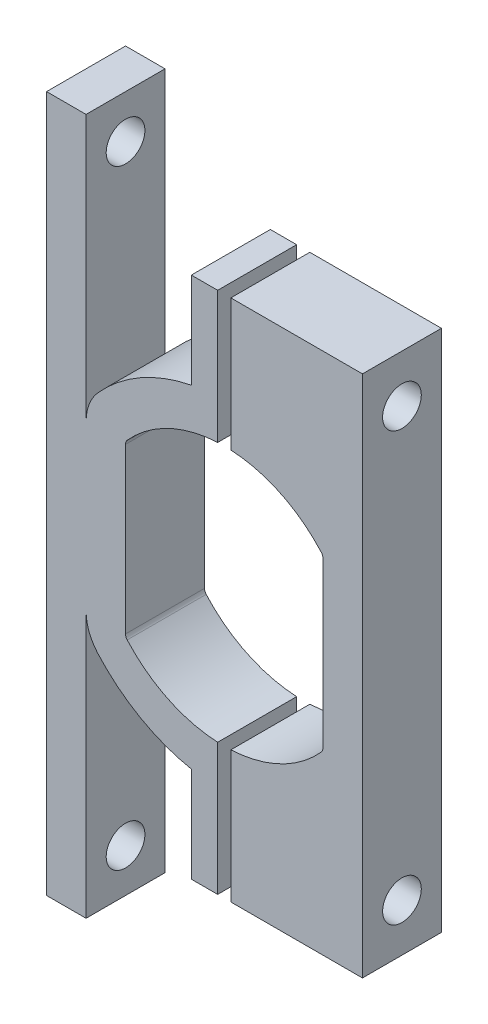
SolidWorks part; units mm, degrees
ref_plane "Front Plane" through (0, 0, 0) normal (0, 0, 1) x (1, 0, 0)
ref_plane "Top Plane" through (0, 0, 0) normal (0, 1, 0) x (1, 0, 0)
ref_plane "Right Plane" through (0, 0, 0) normal (1, 0, 0) x (0, 0, -1)
sketch "Sketch1" plane through (0, 0, 0) normal (0, 0, 1) x (1, 0, 0)
  line L1 (-32.5, -32.5) -> (32.5, -32.5)
  line L2 (-32.5, -32.5) -> (-32.5, 32.5)
  line L3 (-32.5, 32.5) -> (32.5, 32.5)
  line L4 (32.5, -32.5) -> (32.5, 32.5)
  line L5 (-32.5, -32.5) -> (32.5, 32.5) construction
  line L6 (-32.5, 32.5) -> (32.5, -32.5) construction
  point P0 (0, 0)
  dimension "D1" = 65
extrude "Boss-Extrude1" add sketch "Sketch1" along normal blind 6
sketch "Sketch3" plane through (0, 0, 6) normal (0, 0, 1) x (1, 0, 0)
  line L0 (28.5, 4.5979) -> (28.5, 6.2362) construction
  line L1 (28.5, -4.5979) -> (28.5, 4.5979) construction
  line L2 (28.5, -6.2362) -> (28.5, -4.5979) construction
  line L3 (13.5, -4.5979) -> (13.5, -6.2362) construction
  line L4 (13.5, 4.5979) -> (13.5, -4.5979) construction
  line L5 (13.5, 6.2362) -> (13.5, 4.5979) construction
  line L6 (28.5, 4.5979) -> (28.5, 6.2362)
  line L7 (28.5, -4.5979) -> (28.5, 4.5979)
  line L8 (28.5, -6.2362) -> (28.5, -4.5979)
  line L9 (13.5, -4.5979) -> (13.5, -6.2362)
  line L10 (13.5, 4.5979) -> (13.5, -4.5979)
  line L11 (13.5, 6.2362) -> (13.5, 4.5979)
  line L18 (10.5, 6.2362) -> (10.5, 4.5979)
  line L19 (10.5, 4.5979) -> (10.5, -4.5979)
  line L21 (10.5, -4.5979) -> (10.5, -6.2362)
  line L22 (31.5, -6.2362) -> (31.5, -4.5979)
  line L27 (31.5, 4.5979) -> (31.5, 6.2362)
  line L41 (31.5, -4.5979) -> (31.5, 4.5979) construction
  arc A0 (28.5, 6.2362) -> (28.3733, 6.5688) centre (28, 6.2362) ccw construction
  arc A1 (28.3733, -6.5688) -> (28.5, -6.2362) centre (28, -6.2362) ccw construction
  arc A2 (13.6267, -6.5688) -> (28.3733, -6.5688) centre (21, 0) ccw construction
  arc A3 (13.5, -6.2362) -> (13.6267, -6.5688) centre (14, -6.2362) ccw construction
  arc A4 (13.6267, 6.5688) -> (13.5, 6.2362) centre (14, 6.2362) ccw construction
  arc A5 (28.3733, 6.5688) -> (13.6267, 6.5688) centre (21, 0) ccw construction
  arc A6 (28.5, 6.2362) -> (28.3733, 6.5688) centre (28, 6.2362) ccw
  arc A7 (28.3733, -6.5688) -> (28.5, -6.2362) centre (28, -6.2362) ccw
  arc A8 (13.6267, -6.5688) -> (28.3733, -6.5688) centre (21, 0) ccw
  arc A9 (13.5, -6.2362) -> (13.6267, -6.5688) centre (14, -6.2362) ccw
  arc A10 (13.6267, 6.5688) -> (13.5, 6.2362) centre (14, 6.2362) ccw
  arc A11 (28.3733, 6.5688) -> (13.6267, 6.5688) centre (21, 0) ccw
  arc A18 (31.5, 6.2362) -> (30.6133, 8.5644) centre (28, 6.2362) ccw
  arc A19 (30.6133, 8.5644) -> (11.3867, 8.5644) centre (21, 0) ccw
  arc A20 (11.3867, 8.5644) -> (10.5, 6.2362) centre (14, 6.2362) ccw
  arc A21 (10.5, -6.2362) -> (11.3867, -8.5644) centre (14, -6.2362) ccw
  arc A22 (11.3867, -8.5644) -> (30.6133, -8.5644) centre (21, 0) ccw
  arc A23 (30.6133, -8.5644) -> (31.5, -6.2362) centre (28, -6.2362) ccw
  dimension "D1" = 3
extrude "Cut-Extrude2" cut sketch "Sketch3" against normal blind 10
sketch "Sketch4" plane through (0, 0, 0) normal (0, 0, -1) x (-1, 0, 0)
  line L0 (-21, 12.875) -> (-21, 19.875)
  line L1 (-21, 19.875) -> (-18.5, 19.875)
  line L2 (-18.5, 19.875) -> (-18.5, 12.6299)
  line L3 (-31.5, 6.2362) -> (-31.5, 19.875)
  line L4 (-31.5, 19.875) -> (-21, 19.875)
  line L5 (3.3, 0) -> (-3.3, 0) construction
  line L6 (-31.5, -19.875) -> (-21, -19.875)
  line L7 (-31.5, -6.2362) -> (-31.5, -19.875)
  line L8 (-18.5, -19.875) -> (-18.5, -12.6299)
  line L9 (-21, -19.875) -> (-18.5, -19.875)
  line L10 (-21, -12.875) -> (-21, -19.875)
  arc A0 (-11.3867, 8.5644) -> (-30.6133, 8.5644) centre (-21, 0) ccw construction
  arc A1 (-30.6133, 8.5644) -> (-31.5, 6.2362) centre (-28, 6.2362) ccw construction
  arc A2 (-30.6133, 8.5644) -> (-31.5, 6.2362) centre (-28, 6.2362) ccw
  arc A3 (-18.5, 12.6299) -> (-30.6133, 8.5644) centre (-21, 0) ccw
  arc A4 (-30.6133, -8.5644) -> (-31.5, -6.2362) centre (-28, -6.2362) cw
  arc A5 (-18.5, -12.6299) -> (-30.6133, -8.5644) centre (-21, 0) cw
  arc M16 (-30.6133, 8.5644) -> (-31.5, 6.2362) centre (-28, 6.2362) ccw
  arc M23 (-11.3867, 8.5644) -> (-30.6133, 8.5644) centre (-21, 0) ccw
  dimension "D1" = 7
  dimension "D2" = 2.5
extrude "Boss-Extrude2" add sketch "Sketch4" against normal up to surface (6 mm away) contours L4 L3 L0 M16 M23 | L2 L1 L0 M23 | L9 L8 A5 A4 L7 L6 up to face at (21, 0, 6)
sketch "Sketch6" plane through (0, 0, 6) normal (0, 0, 1) x (1, 0, 0)
  line L0 (21, 9.875) -> (21, 19.875)
  line L1 (18.5, 19.875) -> (31.5, 19.875) construction
  line L2 (21.5, 19.875) -> (20.5, 19.875)
  line L3 (21.5, 19.875) -> (21.5, 9.8623)
  line L4 (20.5, 19.875) -> (20.5, 9.8623)
  line L5 (3.3, 0) -> (-3.3, 0) construction
  line L6 (20.5, -19.875) -> (20.5, -9.8623)
  line L7 (21.5, -19.875) -> (21.5, -9.8623)
  line L8 (21.5, -19.875) -> (20.5, -19.875)
  line L9 (21, -9.875) -> (21, -19.875)
  arc A0 (28.3733, 6.5688) -> (13.6267, 6.5688) centre (21, 0) ccw construction
  arc A1 (21.5, 9.8623) -> (20.5, 9.8623) centre (21, 0) ccw
  arc A2 (21.5, -9.8623) -> (20.5, -9.8623) centre (21, 0) cw
  point P11 (21, 19.875)
  dimension "D1" = 1
extrude "Cut-Extrude3" cut sketch "Sketch6" against normal up to body separate body contours L3 A1 L4 L2 | L7 A2 L6 L8
sketch "Sketch7" plane through (18.5, 0, 0) normal (-1, 0, 0) x (0, 0, 1)
  line L0 (6, 12.6299) -> (0, 19.875) construction
  line L1 (3.3, 0) -> (-3.3, 0) construction
  line L2 (6, -12.6299) -> (0, -19.875) construction
  circle A0 centre (3, 16.2525) radius 1.47
  circle A1 centre (3, -16.2525) radius 1.47
  dimension "D1" = 2.94
extrude "Cut-Extrude4" cut sketch "Sketch7" against normal up to surface (13 mm away)
sketch "Sketch8" plane through (10.5, 0, 0) normal (-1, 0, 0) x (0, 0, 1)
  line L0 (3.3, 0) -> (-3.3, 0) construction
  line L1 (0, 6.2362) -> (6, 6.2362)
  line L2 (0, 6.2362) -> (0, -6.2362)
  line L3 (0, -6.2362) -> (6, -6.2362)
  line L4 (6, 6.2362) -> (6, -6.2362)
  line L5 (6, -6.2362) -> (0, -6.2362)
  line L6 (6, -6.2362) -> (6, -26.4475)
  line L7 (6, -26.4475) -> (0, -26.4475)
  line L8 (0, -6.2362) -> (0, -26.4475)
  line L9 (6, -26.4475) -> (0, -19.875) construction
  line L10 (0, 6.2362) -> (0, 26.4475)
  line L11 (6, 6.2362) -> (0, 6.2362)
  line L12 (6, 6.2362) -> (6, 26.4475)
  line L13 (6, -19.875) -> (0, -19.875) construction
  line L14 (6, -19.875) -> (0, -19.875)
  line L15 (6, 26.4475) -> (0, 19.875) construction
  line L16 (6, 19.875) -> (0, 19.875)
  line L17 (6, 26.4475) -> (0, 26.4475)
  circle A0 centre (3, -23.1613) radius 1.47
  circle A1 centre (3, 23.1613) radius 1.47
  line M5 (0, -6.2362) -> (6, -6.2362)
  line M6 (6, -6.2362) -> (6, 6.2362)
  line M7 (6, 6.2362) -> (0, 6.2362)
  line M8 (0, 6.2362) -> (0, -6.2362)
  dimension "D1" = 2.94
extrude "Boss-Extrude3" add sketch "Sketch8" along normal blind 3 contours L6 L14 L8 L7 A0 | L14 L6 L8 M5 | M8 M5 M6 M7 | L12 L16 L10 M7 | L12 L17 L10 L16 A1
